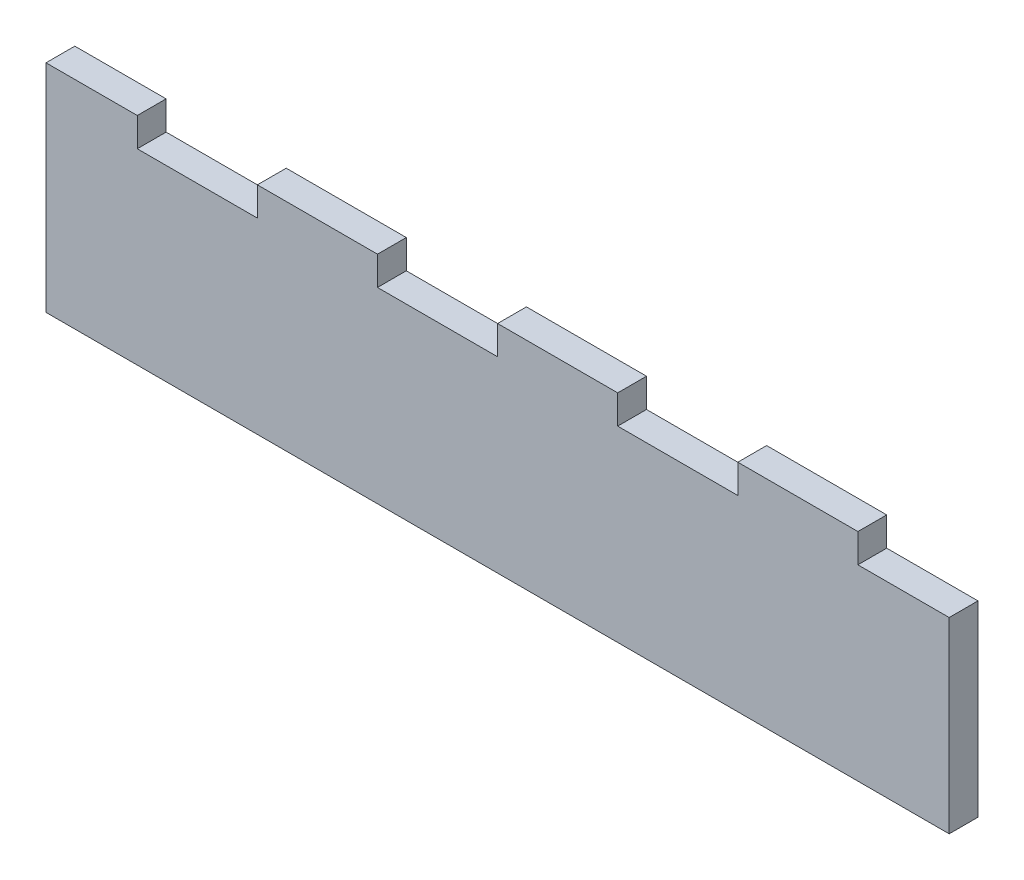
SolidWorks part; units mm, degrees
ref_plane "Plano frontal" through (0, 0, 0) normal (0, 0, 1) x (1, 0, 0)
ref_plane "Plano superior" through (0, 0, 0) normal (0, 1, 0) x (1, 0, 0)
ref_plane "Plano direito" through (0, 0, 0) normal (1, 0, 0) x (0, 0, -1)
sketch "Esboço1" plane through (0, 0, 0) normal (0, 0, 1) x (1, 0, 0)
  line L1 (0, 0) -> (188, 0)
  line L2 (0, 0) -> (0, 39)
  line L3 (19, 39) -> (44, 39)
  line L4 (188, 0) -> (188, 39)
  line L6 (0, 39) -> (0, 45)
  line L7 (0, 45) -> (19, 45)
  line L8 (19, 39) -> (19, 45)
  line L9 (19, 39) -> (44, 39)
  line L14 (44, 39) -> (44, 45)
  line L15 (44, 45) -> (69, 45)
  line L16 (69, 39) -> (69, 45)
  line L17 (94, 39) -> (94, 45)
  line L18 (94, 45) -> (119, 45)
  line L19 (119, 39) -> (119, 45)
  line L21 (144, 39) -> (144, 45)
  line L22 (144, 45) -> (169, 45)
  line L23 (169, 39) -> (169, 45)
  line L24 (69, 39) -> (94, 39)
  line L25 (119, 39) -> (144, 39)
  line L26 (169, 39) -> (188, 39)
  dimension "D1" = 39
  dimension "D2" = 188
  dimension "D3" = 6
  dimension "D4" = 19
  dimension "D6" = 25
  dimension "D7" = 6
  dimension "D8" = 25
  dimension "D9" = 3
extrude "Ressalto-extrusão1" add sketch "Esboço1" along normal blind 6 contours L26 L23 L22 L21 L25 L19 L18 L17 L24 L16 L15 L14 L3 L8 L7 L6 L2 L1 L4
